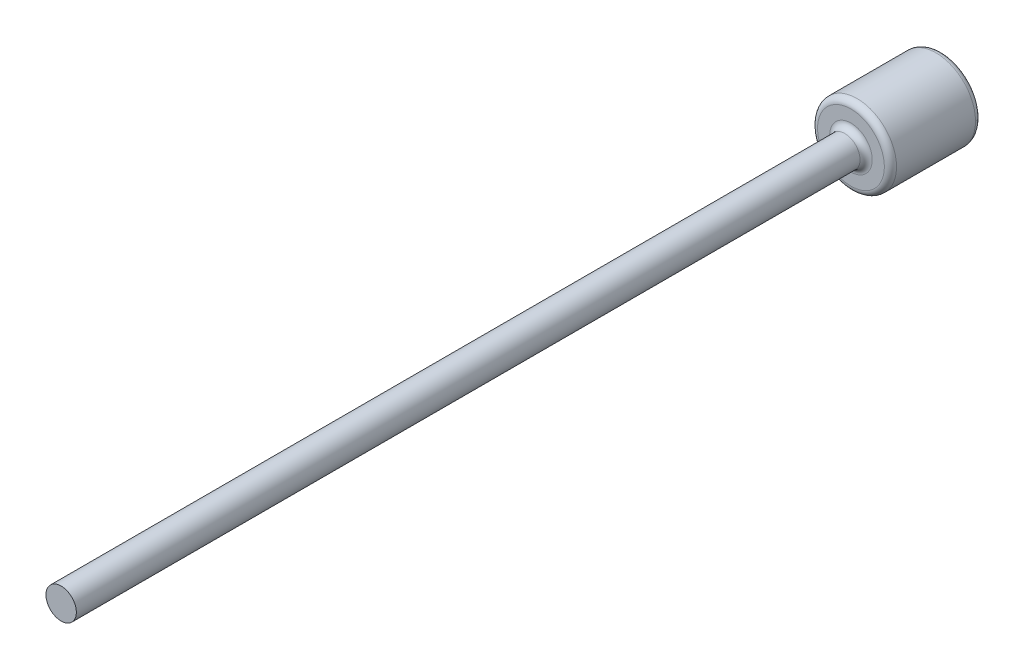
SolidWorks part; units mm, degrees
material "Chrome Stainless Steel"
ref_plane "Front Plane" through (0, 0, 0) normal (0, 0, 1) x (1, 0, 0)
ref_plane "Top Plane" through (0, 0, 0) normal (0, 1, 0) x (1, 0, 0)
ref_plane "Right Plane" through (0, 0, 0) normal (1, 0, 0) x (0, 0, -1)
sketch "Sketch1" plane through (0, 0, 0) normal (0, 0, 1) x (1, 0, 0)
  circle A0 centre (0, 0) radius 13
  dimension "D1" = 26
extrude "Boss-Extrude1" add sketch "Sketch1" against normal blind 30
sketch "Sketch2" plane through (0, 0, 0) normal (0, 0, 1) x (1, 0, 0)
  circle A0 centre (0, 0) radius 5
  dimension "D1" = 10
extrude "Boss-Extrude2" add sketch "Sketch2" along normal blind 240
sketch "Sketch3" plane through (0, 0, 240) normal (0, 0, 1) x (1, 0, 0)
  circle A0 centre (0, 0) radius 5
  dimension "D1" = 10
extrude "Boss-Extrude3" add sketch "Sketch3" along normal blind 20
fillet "Fillet1" radius 2 3 edges at (13, 0, -30) (13, 0, 0) (5, 0, 0)
